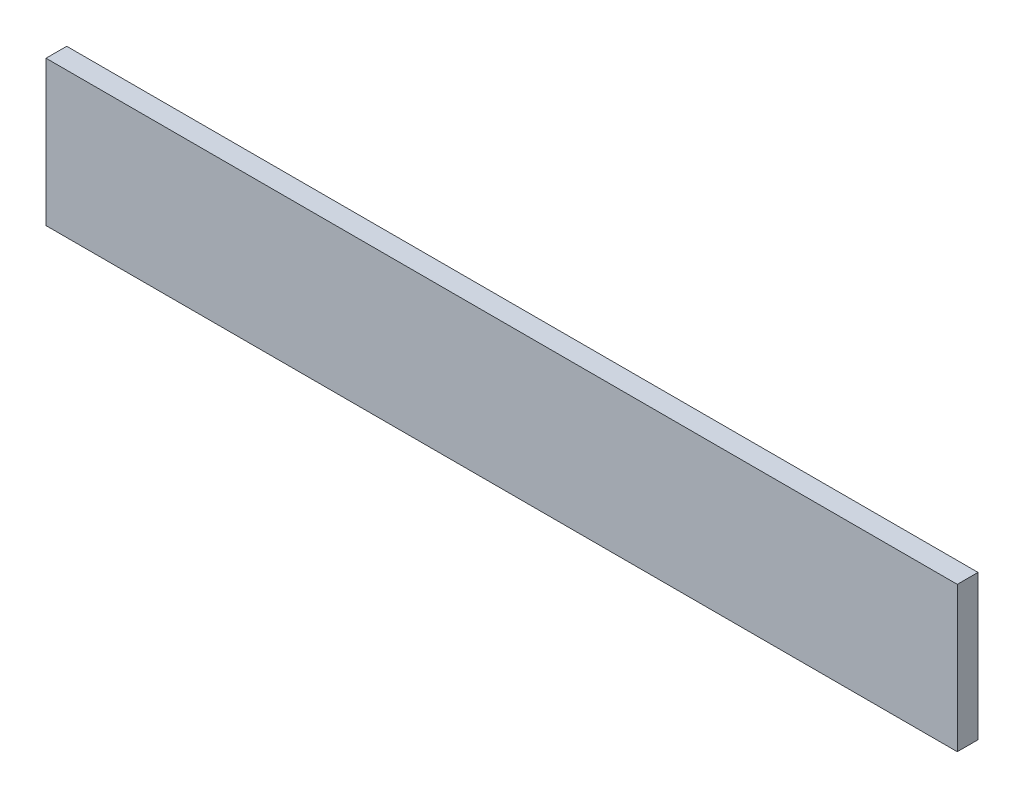
SolidWorks part; units mm, degrees
material "Acrílico (Impacto medio-alto)"
ref_plane "Alzado" through (0, 0, 0) normal (0, 0, 1) x (1, 0, 0)
ref_plane "Planta" through (0, 0, 0) normal (0, 1, 0) x (1, 0, 0)
ref_plane "Vista lateral" through (0, 0, 0) normal (1, 0, 0) x (0, 0, -1)
sketch "Croquis1" plane through (0, 0, 0) normal (0, 0, 1) x (1, 0, 0)
  line L1 (0, 0) -> (220, 0)
  line L2 (0, 0) -> (0, 35)
  line L3 (0, 35) -> (220, 35)
  line L4 (220, 0) -> (220, 35)
  dimension "D1" = 35
  dimension "D2" = 220
extrude "Saliente-Extruir1" add sketch "Croquis1" along normal blind 5
